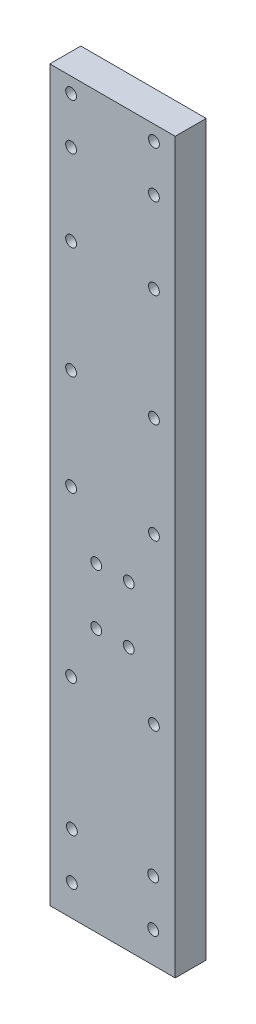
SolidWorks part; units mm, degrees
ref_plane "Front Plane" through (0, 0, 0) normal (0, 0, 1) x (1, 0, 0)
ref_plane "Top Plane" through (0, 0, 0) normal (0, 1, 0) x (1, 0, 0)
ref_plane "Right Plane" through (0, 0, 0) normal (1, 0, 0) x (0, 0, -1)
sketch "Sketch3" plane through (0, 0, 0) normal (0, 0, 1) x (1, 0, 0)
  line L0 (0, 94.0064) -> (0, -0.1536)
  line L1 (16.2, 94.0064) -> (16.2, -0.1536)
  line L2 (0, -0.1536) -> (16.2, -0.1536)
  line L4 (0, 94.0064) -> (16.2, 94.0064)
  line L5 (0, 12.3464) -> (16.2, 12.3464) construction
  line L6 (0, 58.6064) -> (16.2, 58.6064) construction
  line L26 (0, 50.6064) -> (16.2, 50.6064) construction
  line L27 (0, 24.3464) -> (16.2, 24.3464) construction
  line L30 (0, 78.0614) -> (16.2, 78.0614) construction
  line L32 (0, 84.0614) -> (16.2, 84.0614) construction
  circle A0 centre (6, 33.8464) radius 0.7
  circle A1 centre (10.2, 33.8464) radius 0.7
  circle A2 centre (2.75, 86.0614) radius 0.7
  circle A3 centre (10.2, 41.1664) radius 0.7
  circle A4 centre (13.45, 48.1064) radius 0.7
  circle A5 centre (2.75, 92.0614) radius 0.7
  circle A6 centre (13.45, 86.0614) radius 0.7
  circle A7 centre (2.75, 61.1064) radius 0.7
  circle A16 centre (2.85, 9.8464) radius 0.7
  circle A17 centre (13.35, 9.8464) radius 0.7
  circle A18 centre (13.35, 3.8464) radius 0.7
  circle A19 centre (2.85, 3.8464) radius 0.7
  circle A20 centre (13.45, 61.1064) radius 0.7
  circle A21 centre (2.75, 75.5614) radius 0.7
  circle A22 centre (13.45, 26.8464) radius 0.7
  circle A23 centre (13.45, 75.5614) radius 0.7
  circle A24 centre (13.45, 92.0614) radius 0.7
  circle A25 centre (2.75, 26.8464) radius 0.7
  circle A26 centre (6, 41.1064) radius 0.7
  circle A27 centre (2.75, 48.1064) radius 0.7
  dimension "D1" = 2.5
  dimension "D2" = 9.5
  dimension "D32" = 6
  dimension "D33" = 6
  dimension "D45" = 1.4
  dimension "D3" = 2.5
  dimension "D4" = 9.5
  dimension "D5" = 6
  dimension "D6" = 2.75
  dimension "D7" = 2.75
  dimension "D8" = 6
  dimension "D9" = 2.5
  dimension "D10" = 2.5
  dimension "D11" = 9.5
  dimension "D12" = 9.44
  dimension "D13" = 2.75
  dimension "D14" = 6
  dimension "D15" = 2.75
  dimension "D16" = 6
  dimension "D17" = 12
  dimension "D18" = 2.5
  dimension "D19" = 4
  dimension "D20" = 6
  dimension "D21" = 6
  dimension "D22" = 4
  dimension "D23" = 2.85
  dimension "D24" = 2.85
  dimension "D25" = 26.26
  dimension "D26" = 16.2
  dimension "D27" = 8
  dimension "D28" = 2.5
  dimension "D29" = 2.5
  dimension "D30" = 2.75
  dimension "D31" = 2.75
  dimension "D34" = 2.5
  dimension "D35" = 2.5
  dimension "D36" = 2.75
  dimension "D37" = 2.75
  dimension "D38" = 19.455
  dimension "D39" = 6
  dimension "D40" = 2
  dimension "D41" = 2
  dimension "D42" = 2.75
  dimension "D43" = 2.75
  dimension "D44" = 2.5
  dimension "D46" = 2.75
  dimension "D47" = 2.75
  dimension "D48" = 9.945
extrude "Boss-Extrude3" add sketch "Sketch3" along normal blind 4
equation "\"D25@Sketch3\"= \"HL@parametersSketch@prostheticParameters.SLDPRT\" * 0.196 - 4 - 6'Index PIP length"
equation "\"D26@Sketch3\"= \"fingerWidth@parametersSketch@prostheticParameters.SLDPRT\"'Index Width"
equation "\"D38@Sketch3\"= \"HL@parametersSketch@prostheticParameters.SLDPRT\" * 0.143 - 3 - 4 'Index MIP Length"
equation "\"D48@Sketch3\"= \"HL@parametersSketch@prostheticParameters.SLDPRT\" * 0.097 - 3 - 5'Index DIP Length - Gap Fingertip"
equation "\"D45@Sketch3\"= 1 + \"tol1@parametersSketch@prostheticParameters.SLDPRT\""
